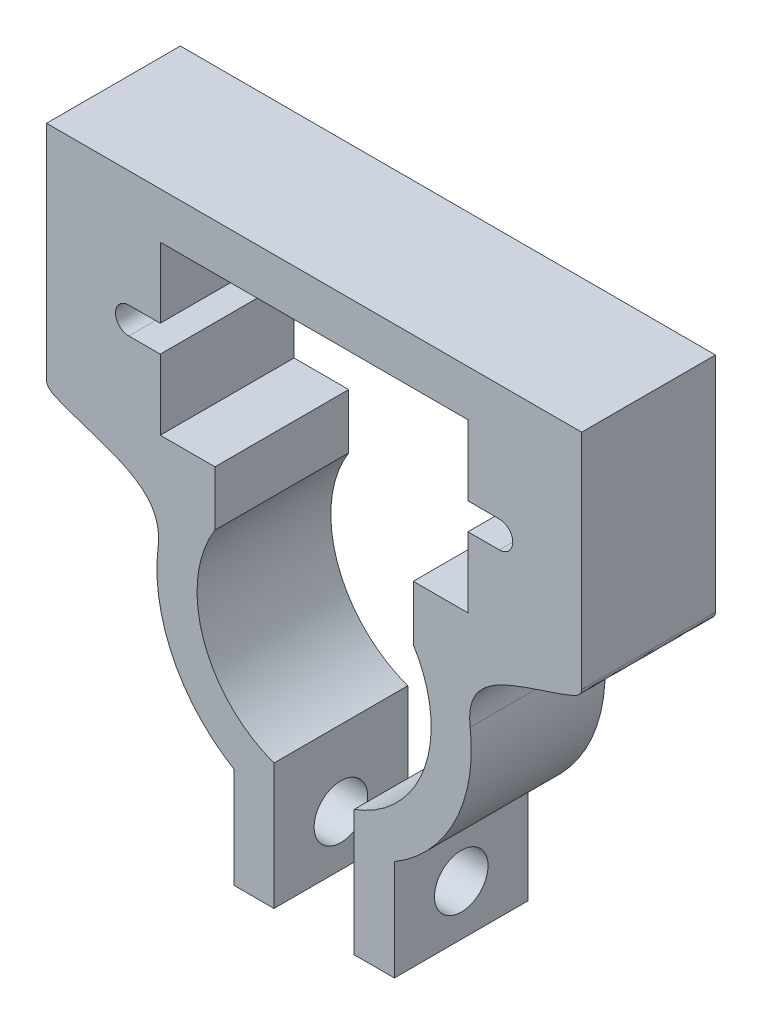
SolidWorks part; units mm, degrees
ref_plane "Alzado" through (0, 0, 0) normal (0, 0, 1) x (1, 0, 0)
ref_plane "Planta" through (0, 0, 0) normal (0, 1, 0) x (1, 0, 0)
ref_plane "Vista lateral" through (0, 0, 0) normal (1, 0, 0) x (0, 0, -1)
sketch "Croquis1" plane through (0, 0, 0) normal (0, 0, 1) x (1, 0, 0)
  line L0 (0, -13.715) -> (0, 24.6969) construction
  line L1 (11.5, 21.25) -> (-11.5, 21.25)
  line L2 (-11.5, 21.25) -> (-11.5, 16)
  line L3 (-11.5, 8.75) -> (-7.4111, 8.75)
  line L4 (-13.0862, 15) -> (13.0862, 15) construction
  line L5 (-13.0862, 15) -> (-27.5017, 15) construction
  line L6 (-13.85, 16) -> (-11.5, 16)
  line L7 (-13.85, 14) -> (-11.5, 14)
  line L8 (31.5623, 8.75) -> (-31.5623, 8.75) construction
  line L9 (-20, 8.0495) -> (-20, 24.6969)
  line L10 (-20, 24.6969) -> (20, 24.6969)
  line L11 (-11.5, 14) -> (-11.5, 8.75)
  line L12 (-6, -10.1026) -> (-6, -17.637)
  line L13 (-6, -17.637) -> (-3, -17.637)
  line L14 (-3, -17.637) -> (-3, -8.2196)
  line L15 (-7.4111, 8.75) -> (-7.4111, 4.6517)
  line L16 (13.0862, 15) -> (27.5017, 15) construction
  line L17 (7.4111, 8.75) -> (7.4111, 4.6517)
  line L18 (3, -17.637) -> (3, -8.2196)
  line L19 (6, -17.637) -> (3, -17.637)
  line L20 (6, -10.1026) -> (6, -17.637)
  line L21 (11.5, 14) -> (11.5, 8.75)
  line L22 (20, 8.0495) -> (20, 24.6969)
  line L23 (13.85, 14) -> (11.5, 14)
  line L24 (13.85, 16) -> (11.5, 16)
  line L25 (11.5, 8.75) -> (7.4111, 8.75)
  line L26 (11.5, 21.25) -> (11.5, 16)
  line L27 (4.69, 21.25) -> (4.69, 8.75) construction
  arc A0 (-13.85, 16) -> (-13.85, 14) centre (-13.85, 15) ccw
  arc A1 (-3, -8.2196) -> (-7.4111, 4.6517) centre (0, 0) cw
  arc A2 (-6, -10.1026) -> (-11.6628, 1.4289) centre (0, 0) cw
  arc A3 (6, -10.1026) -> (11.6628, 1.4289) centre (0, 0) ccw
  arc A4 (3, -8.2196) -> (7.4111, 4.6517) centre (0, 0) ccw
  arc A5 (13.85, 16) -> (13.85, 14) centre (13.85, 15) cw
  spline S0 degree 3 poles (-20, 8.0495) (-20, 7.5834) (-15.9235, 5.8469) (-11.1933, 5.2613) (-11.6628, 1.4289) knots 0 0 0 0 0.136186 1 1 1 1
  spline S1 degree 3 poles (20, 8.0495) (20, 7.5834) (15.9235, 5.8469) (11.1933, 5.2613) (11.6628, 1.4289) knots 0 0 0 0 0.136186 1 1 1 1
  point P3 (-11.5, 18.625)
  point P14 (-6, -13.8698)
  point P29 (4.69, 15)
  point P30 (0, 8.75)
  point P33 (0, 15)
  point P51 (0, 21.25)
  point P52 (11.5, 18.625)
  dimension "D4" = 8.75
  dimension "D3" = 1
  dimension "D6" = 3
  dimension "D1" = 12.5
  dimension "D2" = 11.5
  dimension "D5" = 2.35
  dimension "D7" = 3
  dimension "D8" = 20
  dimension "D9" = 3
  dimension "D10" = 3.4469
  dimension "D11" = 23
extrude "Saliente-Extruir1" add sketch "Croquis1" along normal blind 10
sketch "Croquis2" plane through (-6, 0, 0) normal (-1, 0, 0) x (0, 0, 1)
  line L0 (0, -13.8698) -> (10, -13.8698) construction
  line L1 (0, -10.1026) -> (0, -17.637) construction
  line L2 (10, -10.1026) -> (10, -17.637) construction
  line L3 (5, -10.1026) -> (5, -17.637) construction
  line L4 (10, -10.1026) -> (0, -10.1026) construction
  line L5 (10, -17.637) -> (0, -17.637) construction
  circle A0 centre (5, -13.8698) radius 2
  dimension "D1" = 4
extrude "Cortar-Extruir1" cut sketch "Croquis2" against normal through all
